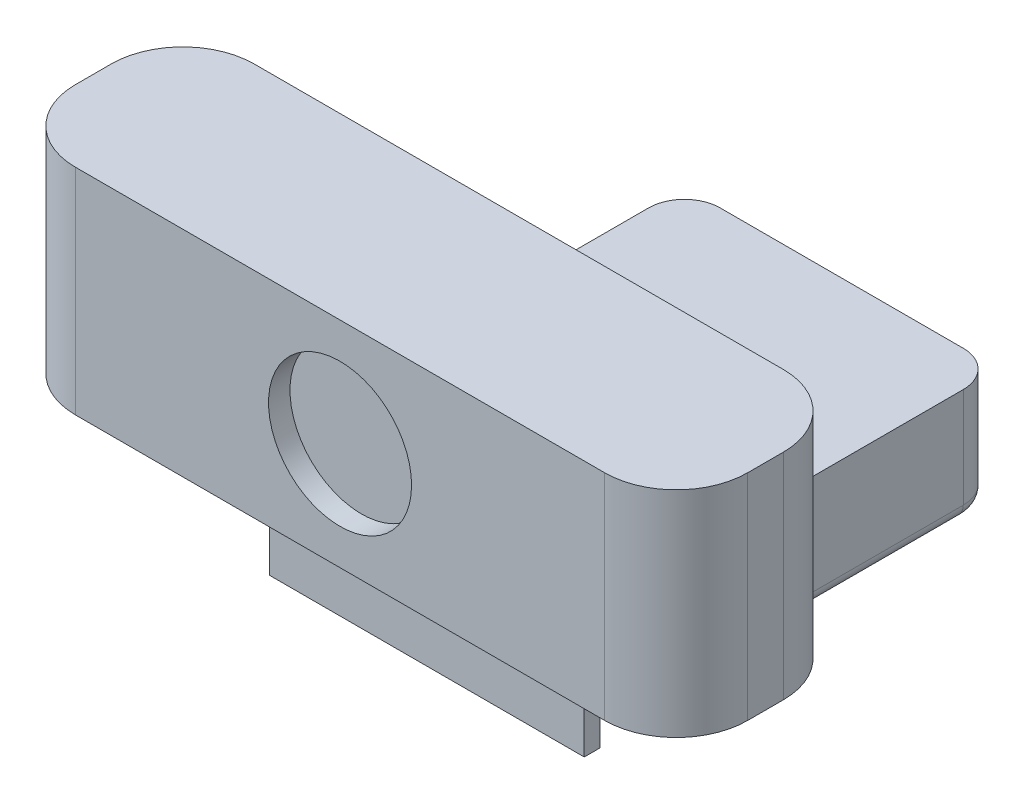
SolidWorks part; units mm, degrees
ref_plane "Front" through (0, 0, 0) normal (0, 0, 1) x (1, 0, 0)
ref_plane "Top" through (0, 0, 0) normal (0, 1, 0) x (1, 0, 0)
ref_plane "Right" through (0, 0, 0) normal (1, 0, 0) x (0, 0, -1)
sketch "Sketch1" plane through (0, 0, 0) normal (0, 1, 0) x (1, 0, 0)
  line L1 (-22, 25) -> (22, 25)
  line L2 (-22, 25) -> (-22, -25)
  line L3 (-22, -25) -> (22, -25)
  line L4 (22, 25) -> (22, -25)
  line L5 (-22, 25) -> (22, -25) construction
  line L6 (-22, -25) -> (22, 25) construction
  point P0 (0, 0)
  dimension "D1" = 44
  dimension "D2" = 50
extrude "Boss-Extrude1" add sketch "Sketch1" along normal blind 10
sketch "Sketch2" plane through (22, 0, 0) normal (1, 0, 0) x (0, 0, -1)
  line L0 (25, 10) -> (25, 0) construction
  line L1 (25, 10) -> (-30.8, 10)
  line L2 (25, 10) -> (25, 16)
  line L3 (25, 16) -> (-33, 16)
  line L4 (-33, 10) -> (-33, 16)
  line L6 (-33, 10) -> (-33, -2)
  line L7 (-33, -2) -> (-30.8, -2)
  line L8 (-30.8, 10) -> (-30.8, -2)
  dimension "D1" = 58
  dimension "D2" = 2.2
  dimension "D3" = 6
  dimension "D4" = 12
extrude "Boss-Extrude2" add sketch "Sketch2" against normal up to surface (44 mm away) up to face at (-22, 5, 0)
fillet "Fillet1" radius 5 4 edges at (-22, 5, 25) (-22, 8, -25) (22, 8, -25) (22, 5, 25)
sketch "Sketch3" plane through (0, 16, 0) normal (0, 1, 0) x (1, 0, 0)
  line L0 (0, 13.6744) -> (0, -37.458) construction
  line L2 (-47, -20.1473) -> (47, -20.1473)
  line L3 (-47, -20.1473) -> (-47, -45.1473)
  line L4 (-47, -45.1473) -> (47, -45.1473)
  line L5 (47, -20.1473) -> (47, -45.1473)
  line L6 (-47, -20.1473) -> (47, -45.1473) construction
  line L7 (-47, -45.1473) -> (47, -20.1473) construction
  point P3 (0, -32.6473)
  dimension "D1" = 94
  dimension "D2" = 25
extrude "Boss-Extrude3" add sketch "Sketch3" along normal blind 30
fillet "Fillet2" radius 10 4 edges at (-47, 31, 20.1473) (-47, 31, 45.1473) (47, 31, 20.1473) (47, 31, 45.1473)
sketch "Sketch4" plane through (0, 0, 45.1473) normal (0, 0, 1) x (1, 0, 0)
  line L2 (-22, 16) -> (22, 16) construction
  circle A0 centre (0, 31) radius 10
  point P6 (0, 0)
  dimension "D1" = 20
  dimension "D2" = 15
extrude "Cut-Extrude1" cut sketch "Sketch4" against normal blind 3
sketch "Sketch5" plane through (0, 0, 0) normal (0, -1, 0) x (1, 0, 0)
  line L0 (-17, 25) -> (17, 25) construction
  circle A0 centre (0, 5) radius 2.5
  point P2 (0, 0)
  dimension "D1" = 5
  dimension "D2" = 20
extrude "Cut-Extrude2" cut sketch "Sketch5" against normal blind 10
chamfer "Chamfer1" distance 1 angle 45 1 edges at (0, 0, 2.5)
fillet "Fillet3" radius 2 9 edges at (20.5355, 0, 23.5355) (22, 0, 0) (20.5355, 0, -23.5355) (0, 0, -25) (-20.5355, 0, -23.5355) (-22, 0, 0) (-20.5355, 0, 23.5355) (0, 0, 25) (0, 0, 8.5)
